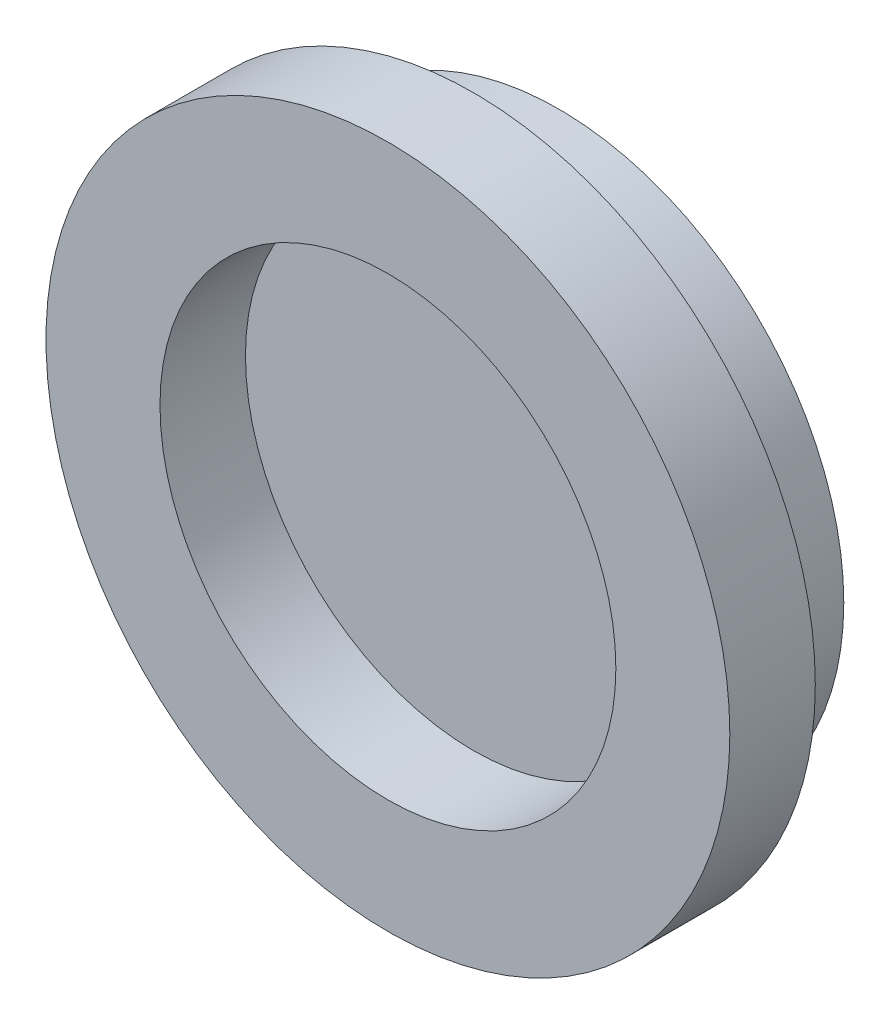
SolidWorks part; units mm, degrees
ref_plane "Front Plane" through (0, 0, 0) normal (0, 0, 1) x (1, 0, 0)
ref_plane "Top Plane" through (0, 0, 0) normal (0, 1, 0) x (1, 0, 0)
ref_plane "Right Plane" through (0, 0, 0) normal (1, 0, 0) x (0, 0, -1)
sketch "Sketch1" plane through (0, 0, 0) normal (0, 0, 1) x (1, 0, 0)
  circle A0 centre (0, 0) radius 10
extrude "Boss-Extrude1" add sketch "Sketch1" along normal blind 3
sketch "Sketch2" plane through (0, 0, 3) normal (0, 0, 1) x (1, 0, 0)
  circle A0 centre (0, 0) radius 8
  circle A1 centre (0, 0) radius 12
extrude "Boss-Extrude2" add sketch "Sketch2" along normal blind 3
